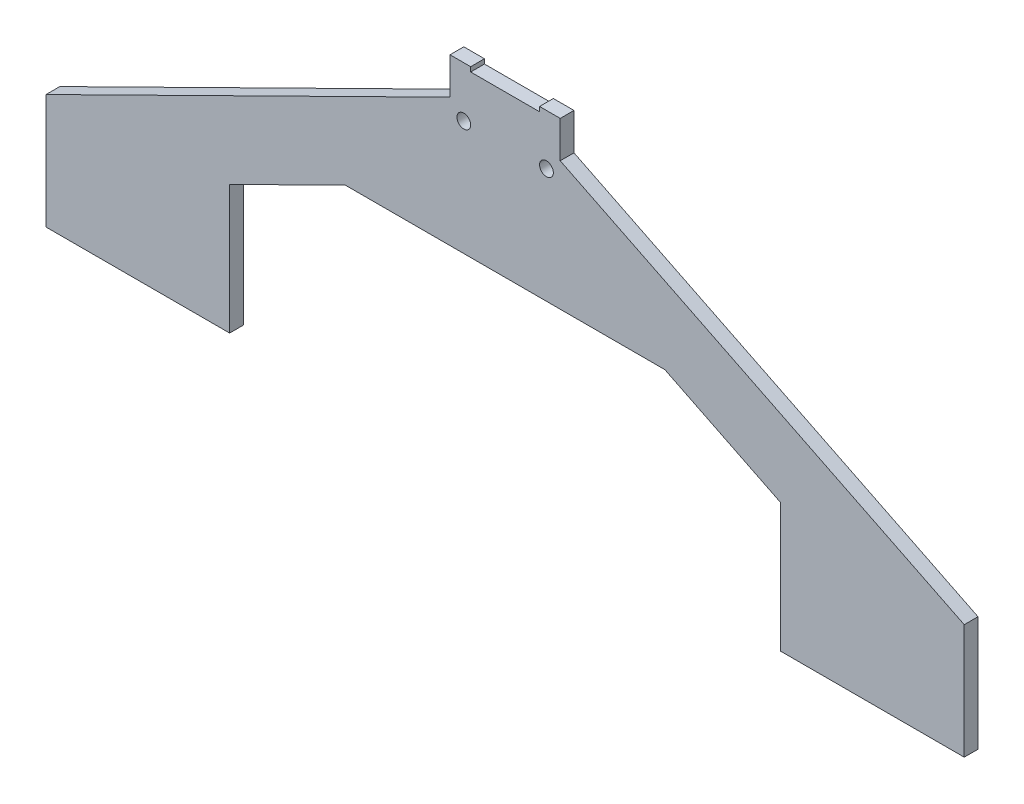
SolidWorks part; units mm, degrees
ref_plane "前视基准面" through (0, 0, 0) normal (0, 0, 1) x (1, 0, 0)
ref_plane "上视基准面" through (0, 0, 0) normal (0, 1, 0) x (1, 0, 0)
ref_plane "右视基准面" through (0, 0, 0) normal (1, 0, 0) x (0, 0, -1)
sketch "草图2" plane through (356.18, -2895.5282, -3033.9812) normal (0, 0, 1) x (1, 0, 0)
  line L0 (-296.18, 2848.0684) -> (-321.3861, 2860.5282)
  line L2 (-368.18, 2896.5282) -> (-363.68, 2896.5282)
  line L6 (-363.68, 2896.5282) -> (-363.68, 2895.5282)
  line L8 (-368.18, 2896.5282) -> (-368.18, 2888.5282)
  line L9 (-368.18, 2888.5282) -> (-456.18, 2845.0282)
  line L10 (-456.18, 2845.0282) -> (-456.18, 2820.0282)
  line L11 (-456.18, 2820.0282) -> (-416.18, 2820.0282)
  line L12 (-416.18, 2820.0282) -> (-416.18, 2848.0684)
  line L13 (-416.18, 2848.0684) -> (-390.9739, 2860.5282)
  line L14 (-390.9739, 2860.5282) -> (-321.3861, 2860.5282)
  line L15 (-356.18, 2895.5282) -> (-356.18, 2860.5282) construction
  line L16 (-363.68, 2895.5282) -> (-348.68, 2895.5282)
  line L17 (-296.18, 2820.0282) -> (-296.18, 2848.0684)
  line L18 (-256.18, 2820.0282) -> (-296.18, 2820.0282)
  line L19 (-256.18, 2845.0282) -> (-256.18, 2820.0282)
  line L20 (-344.18, 2888.5282) -> (-256.18, 2845.0282)
  line L21 (-344.18, 2896.5282) -> (-344.18, 2888.5282)
  line L22 (-348.68, 2895.5282) -> (-348.68, 2896.5282)
  line L23 (-348.68, 2896.5282) -> (-344.18, 2896.5282)
  point P5 (-356.18, 2895.5282)
  dimension "D1" = 24
  dimension "D2" = 200
  dimension "D3" = 40
  dimension "D4" = 25
  dimension "D5" = 8
  dimension "D6" = 1
  dimension "D7" = 15
  dimension "D8" = 15
  dimension "D9" = 75.5
  dimension "D10" = 36
extrude "凸台-拉伸1" add sketch "草图2" along normal blind 3
sketch "草图3" plane through (0, 0, -3030.9812) normal (0, 0, 1) x (1, 0, 0)
  line L0 (7.5, 0) -> (-7.5, 0) construction
  line L1 (-9, -10) -> (9, -10) construction
  circle A0 centre (9, -10) radius 1.5
  circle A1 centre (-9, -10) radius 1.5
  point P6 (0, -10)
  dimension "D3" = 3
  dimension "D1" = 18
  dimension "D2" = 10
extrude "切除-拉伸1" cut sketch "草图3" against normal blind 3
